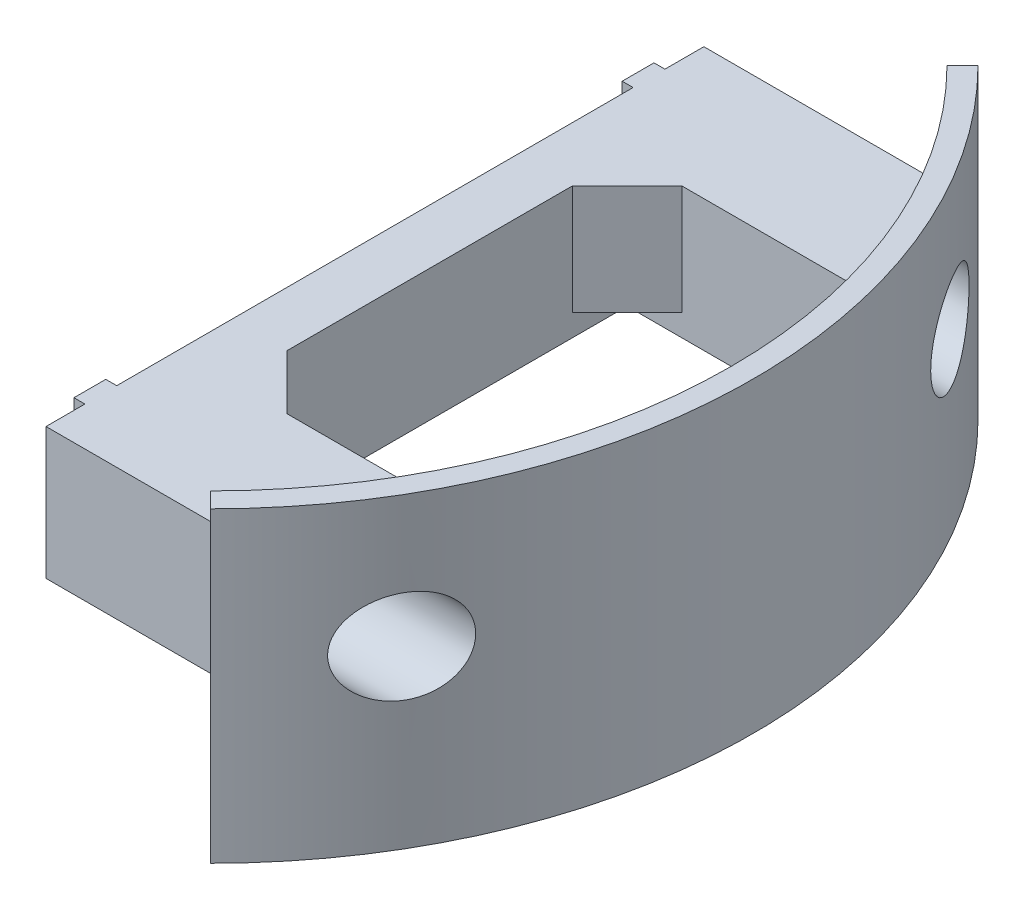
SolidWorks part; units mm, degrees
ref_plane "Front Plane" through (0, 0, 0) normal (0, 0, 1) x (1, 0, 0)
ref_plane "Top Plane" through (0, 0, 0) normal (0, 1, 0) x (1, 0, 0)
ref_plane "Right Plane" through (0, 0, 0) normal (1, 0, 0) x (0, 0, -1)
ref_axis "Axis1" through (0, -0.2847, 0) along (0, 1, 0)
ref_plane "SupportPlain" through (0, 10, 0) normal (0, 1, 0) x (1, 0, 0)
sketch "Sketch1" plane through (0, 0, 0) normal (0, 0, 1) x (1, 0, 0)
  line L0 (49.5, 0) -> (49.5, 40)
  line L5 (49.5, 40) -> (47.5, 40)
  line L6 (47.5, 40) -> (47.5, 0)
  line L7 (47.5, 0) -> (49.5, 0)
  point P9 (48.5, 0)
  dimension "D1" = 40
  dimension "D2" = 2
  dimension "D3" = 49.5
revolve "Main" add sketch "Sketch1" angle 90 mid plane about axis through (0, -0.2847, 0) along (0, 1, 0)
sketch "Sketch2" plane through (0, 10, 0) normal (0, -1, 0) x (-1, 0, 0)
  line L0 (-43.9574, -18) -> (-20, -18)
  line L1 (-36.8273, -30) -> (-15, -30)
  line L2 (-33.5876, -33.5876) -> (-33.5876, 33.5876) construction
  line L9 (-43.9574, 18) -> (-20, 18)
  line L10 (-15, -30) -> (-15, 30)
  line L11 (-15, 30) -> (-36.8273, 30)
  line L13 (-20, 18) -> (-20, -18)
  arc A0 (-43.9574, 18) -> (-36.8273, 30) centre (0, 0) cw
  circle A1 centre (0, 0) radius 50 construction
  arc A2 (-36.8273, -30) -> (-43.9574, -18) centre (0, 0) cw
  circle A3 centre (0, 0) radius 47.5 construction
  point P4 (0, 0)
  point P7 (0, 0)
  point P26 (-15, 0)
  dimension "D7" = 12
  dimension "D4" = 100
  dimension "D1" = 12
  dimension "D2" = 15
  dimension "D3" = 5
  dimension "D5" = 60
extrude "Support" add sketch "Sketch2" against normal blind 12
sketch "Sketch6" plane through (0, 10, 0) normal (0, 1, 0) x (1, 0, 0)
  line L0 (15, -30) -> (15, 30) construction
  line L1 (14, -23.55) -> (15, -23.55)
  line L2 (14, -23.55) -> (14, -26.45)
  line L3 (14, -26.45) -> (15, -26.45)
  line L4 (15, -23.55) -> (15, -26.45)
  line L6 (14, 26.45) -> (15, 26.45)
  line L7 (14, 26.45) -> (14, 23.55)
  line L8 (14, 23.55) -> (15, 23.55)
  line L9 (15, 26.45) -> (15, 23.55)
  line L11 (15, -30) -> (15, 30) construction
  point P10 (15, -30)
  point P13 (15, 30)
  dimension "D1" = 3.55
  dimension "D2" = 2.9
  dimension "D3" = 1
  dimension "D4" = 3.55
extrude "Fix" add sketch "Sketch6" along normal up to surface (12 mm away) up to face at (29.057, 22, 0)
sketch "Sketch9" plane through (20, 0, 0) normal (1, 0, 0) x (0, 0, -1)
  line L1 (30, 22) -> (30, 10) construction
  line L2 (-30, 22) -> (-30, 10) construction
  line L3 (30, 22) -> (30, 10) construction
  line L4 (-30, 42) -> (30, 42)
  line L5 (-30, 42) -> (-30, 34)
  line L6 (-30, 34) -> (30, 34)
  line L7 (30, 42) -> (30, 34)
  line L8 (-30, 22) -> (-30, 10) construction
  line L9 (-23.55, 10) -> (23.55, 10) construction
  circle A0 centre (25, 16) radius 1.6
  circle A1 centre (-25, 16) radius 1.6
  point P4 (30, 16)
  point P5 (0, 0)
  dimension "D1" = 3.2
  dimension "D2" = 3.2
  dimension "D4" = 5
  dimension "D5" = 5
  dimension "D6" = 8
  dimension "D7" = 24
extrude "Holes" cut sketch "Sketch9" against normal through all
sketch "Sketch10" plane through (20, 0, 0) normal (1, 0, 0) x (0, 0, -1)
  circle A0 centre (25, 16) radius 4.25
  circle A1 centre (-25, 16) radius 4.25
  arc A2 (23.55, 15.3236) -> (26.45, 15.3236) centre (25, 16) ccw construction
  arc A3 (-26.45, 15.3236) -> (-23.55, 15.3236) centre (-25, 16) ccw construction
  dimension "D1" = 8.5
extrude "BigHoles" cut sketch "Sketch10" along normal through all
sketch "Sketch11" plane through (0, 22, 0) normal (0, 1, 0) x (1, 0, 0)
  line L0 (20, 18) -> (25, 18)
  line L2 (25, 18) -> (20, 13)
  line L3 (20, 18) -> (20, -18) construction
  line L4 (20, 13) -> (20, 18)
  line L5 (20, -18) -> (20, -13)
  line L6 (20, -13) -> (25, -18)
  line L7 (20, -18) -> (43.9574, -18) construction
  line L8 (25, -18) -> (20, -18)
  line L9 (41.1113, 18) -> (46.1113, 18)
  line L10 (46.1113, 18) -> (46.1113, 13)
  line L11 (46.1113, 13) -> (41.1113, 18)
  line L12 (41.1113, -18) -> (46.1113, -18)
  line L13 (46.1113, -18) -> (46.1113, -11.4018)
  line L14 (46.1113, -11.4018) -> (41.1113, -18)
  line L15 (43.9574, 18) -> (20, 18) construction
  arc A0 (35.0018, -35.0018) -> (35.0018, 35.0018) centre (0, 0) ccw construction
  arc A1 (33.5876, -33.5876) -> (33.5876, 33.5876) centre (0, 0) ccw construction
  point P3 (20, 18)
  point P4 (45.2797, 17.657)
  point P22 (0, 0)
  point P27 (20, 20)
  point P28 (40.2797, 18)
  dimension "D1" = 5
  dimension "D2" = 5
  dimension "D3" = 5
extrude "Reinforcement" add sketch "Sketch11" against normal blind 10
sketch "Sketch12" plane through (15, 0, 0) normal (-1, 0, 0) x (0, 0, 1)
  line L1 (-35.0018, 28) -> (35.0018, 28)
  line L2 (-35.0018, 28) -> (-35.0018, 40)
  line L3 (-35.0018, 40) -> (35.0018, 40)
  line L4 (35.0018, 28) -> (35.0018, 40)
  line L6 (23.55, 22) -> (-23.55, 22) construction
  line L7 (35.0018, 40) -> (-35.0018, 40) construction
  line L8 (-35.0018, 0) -> (-35.0018, 40) construction
  line L9 (35.0018, 0) -> (35.0018, 40) construction
  point P8 (-30, 29.4148)
  dimension "D1" = 6
  dimension "D2" = 12
  dimension "D3" = 0
extrude "SensorWindow" cut sketch "Sketch12" against normal through all
